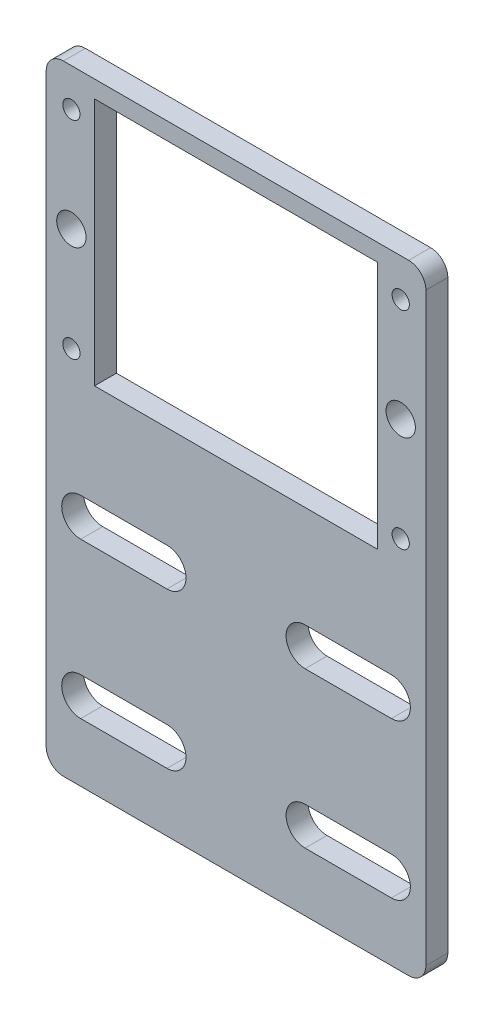
SolidWorks part; units mm, degrees
ref_plane "Front Plane" through (0, 0, 0) normal (0, 0, 1) x (1, 0, 0)
ref_plane "Top Plane" through (0, 0, 0) normal (0, 1, 0) x (1, 0, 0)
ref_plane "Right Plane" through (0, 0, 0) normal (1, 0, 0) x (0, 0, -1)
sketch "Sketch1" plane through (0, 0, 0) normal (0, 0, 1) x (1, 0, 0)
  line L1 (0, 0) -> (110, 0)
  line L2 (0, 0) -> (0, 82)
  line L3 (0, 82) -> (110, 82)
  line L4 (110, 0) -> (110, 82)
  dimension "D1" = 110
  dimension "D2" = 82
extrude "Boss-Extrude1" add sketch "Sketch1" along normal blind 6.35
sketch "Sketch2" plane through (0, 0, 6.35) normal (0, 0, 1) x (1, 0, 0)
  line L0 (55, 82) -> (55, 0) construction
  line L1 (110, 82) -> (0, 82) construction
  line L2 (0, 0) -> (110, 0) construction
  line L3 (0, 41) -> (110, 41) construction
  line L4 (0, 82) -> (0, 0) construction
  line L5 (110, 0) -> (110, 82) construction
  line L7 (14, 5) -> (96, 5)
  line L8 (14, 5) -> (14, 77)
  line L9 (14, 77) -> (96, 77)
  line L10 (96, 5) -> (96, 77)
  line L11 (14, 5) -> (96, 77) construction
  line L12 (14, 77) -> (96, 5) construction
  point P12 (55, 41)
  dimension "D1" = 14
  dimension "D2" = 5
extrude "Cut-Extrude1" cut sketch "Sketch2" against normal up to next
sketch "Sketch3" plane through (0, 0, 6.35) normal (0, 0, 1) x (1, 0, 0)
  line L0 (0, 0) -> (110, 0) construction
  line L1 (0, 0) -> (110, 0)
  line L2 (0, 0) -> (0, -97.4643)
  line L3 (0, -97.4643) -> (110, -97.4643)
  line L4 (110, 0) -> (110, -97.4643)
  line L5 (110, 0) -> (110, 82) construction
  point P6 (55, 0)
extrude "Boss-Extrude2" add sketch "Sketch3" against normal up to surface (6.35 mm away) up to face at (55, 41, 0)
sketch "Sketch4" plane through (0, 0, 6.35) normal (0, 0, 1) x (1, 0, 0)
  line L0 (10, -74.9643) -> (35, -74.9643) construction
  line L3 (55, 5) -> (55, -97.4643) construction
  line L4 (14, 5) -> (96, 5) construction
  line L5 (0, -97.4643) -> (110, -97.4643) construction
  line L6 (10, -69.4643) -> (35, -69.4643)
  line L7 (10, -80.4643) -> (35, -80.4643)
  line L8 (100, -74.9643) -> (75, -74.9643) construction
  line L9 (100, -69.4643) -> (75, -69.4643)
  line L12 (10, -29.9643) -> (35, -29.9643) construction
  line L13 (10, -35.4643) -> (35, -35.4643)
  line L14 (10, -24.4643) -> (35, -24.4643)
  line L15 (100, -80.4643) -> (75, -80.4643)
  line L18 (0, -52.4643) -> (110, -52.4643) construction
  line L19 (0, 82) -> (0, -97.4643) construction
  line L20 (110, -97.4643) -> (110, 82) construction
  line L21 (0, -97.4643) -> (110, -97.4643) construction
  line L22 (100, -29.9643) -> (75, -29.9643) construction
  line L23 (100, -35.4643) -> (75, -35.4643)
  line L24 (100, -24.4643) -> (75, -24.4643)
  arc A4 (10, -35.4643) -> (10, -24.4643) centre (10, -29.9643) cw
  arc A5 (35, -24.4643) -> (35, -35.4643) centre (35, -29.9643) cw
  arc A6 (10, -69.4643) -> (10, -80.4643) centre (10, -74.9643) ccw
  arc A7 (35, -80.4643) -> (35, -69.4643) centre (35, -74.9643) ccw
  arc A8 (100, -69.4643) -> (100, -80.4643) centre (100, -74.9643) cw
  arc A9 (75, -80.4643) -> (75, -69.4643) centre (75, -74.9643) cw
  arc A10 (100, -35.4643) -> (100, -24.4643) centre (100, -29.9643) ccw
  arc A11 (75, -24.4643) -> (75, -35.4643) centre (75, -29.9643) ccw
  point P0 (0, 0)
  point P3 (22.5, -74.9643)
  point P16 (87.5, -74.9643)
  point P23 (87.5, -29.9643)
  point P28 (22.5, -29.9643)
  dimension "D1" = 45
  dimension "D2" = 20
  dimension "D3" = 45
  dimension "D4" = 22.5
extrude "Cut-Extrude2" cut sketch "Sketch4" against normal up to next
fillet "Fillet1" radius 5 4 edges at (110, 82, 3.175) (0, 82, 3.175) (0, -97.4643, 3.175) (110, -97.4643, 3.175)
sketch "Sketch5" plane through (0, 0, 6.35) normal (0, 0, 1) x (1, 0, 0)
  line L0 (14, 41) -> (96, 41) construction
  line L1 (14, 77) -> (14, 5) construction
  line L2 (96, 5) -> (96, 77) construction
  line L3 (55, 5) -> (55, 77) construction
  line L4 (14, 5) -> (96, 5) construction
  line L5 (96, 77) -> (14, 77) construction
  circle A0 centre (7.2988, 11.0026) radius 2.5019
  circle A1 centre (7.2988, 70.9974) radius 2.5019
  circle A2 centre (102.7012, 70.9974) radius 2.5019
  circle A3 centre (102.7012, 11.0026) radius 2.5019
  circle A4 centre (7.2988, 41) radius 4.25
  circle A5 centre (102.7012, 41) radius 4.25
  dimension "D3" = 5.0038
  dimension "D1" = 29.9974
  dimension "D2" = 47.7012
extrude "Cut-Extrude3" cut sketch "Sketch5" against normal up to next
